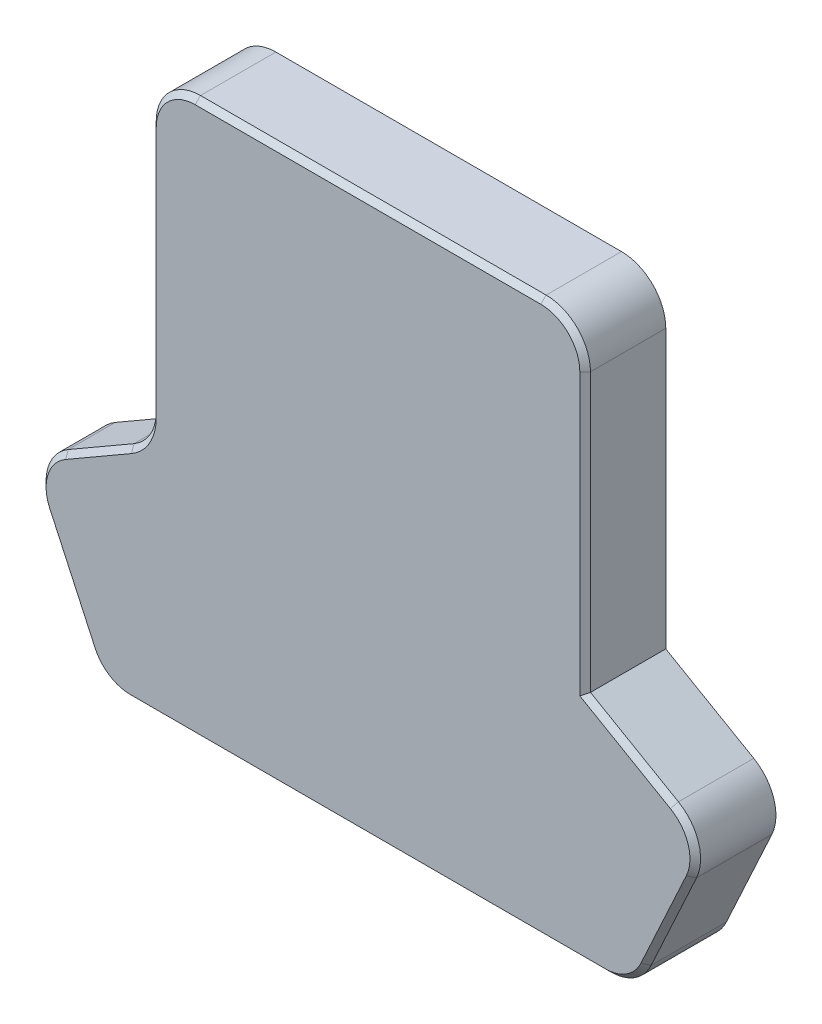
SolidWorks part; units mm, degrees
ref_plane "Front Plane" through (0, 0, 0) normal (0, 0, 1) x (1, 0, 0)
ref_plane "Top Plane" through (0, 0, 0) normal (0, 1, 0) x (1, 0, 0)
ref_plane "Right Plane" through (0, 0, 0) normal (1, 0, 0) x (0, 0, -1)
sketch "Sketch1" plane through (0, 0, 0) normal (0, 0, 1) x (1, 0, 0)
  line L0 (-54.5, 42.45) -> (-12.4, 42.45)
  line L1 (-54.5, 29.0597) -> (-54.5, 57.5) construction
  line L2 (-12.4, 42.45) -> (-12.4, 7.25)
  line L3 (-12.4, 7.25) -> (-63.3441, 7.25)
  line L4 (-60, 0) -> (-68.3768, 18.1612) construction
  line L5 (-54.5, 42.45) -> (-54.5, 62.5)
  line L6 (-54.5, 62.5) -> (-5.5, 62.5)
  line L7 (-5.5, 62.5) -> (-5.5, 26.173)
  line L8 (-5.5, 26.173) -> (8.3768, 18.1612)
  line L9 (8.3768, 18.1612) -> (0, 0)
  line L10 (0, 0) -> (-60, 0)
  line L11 (-60, 0) -> (-63.3441, 7.25)
  line L12 (-71.5, 7.35) -> (-13.5, 7.35) construction
  line L13 (-3, 24.7296) -> (4.4256, 20.4425) construction
  line L14 (0, 0) -> (8.3768, 18.1612) construction
  line L16 (-12.5, 8.35) -> (-12.5, 41.35) construction
  line L17 (-13.5, 42.35) -> (-71.5, 42.35) construction
  point P14 (0, 0)
  point P15 (4.5312, 0)
  dimension "D1" = 0.1
  dimension "0.1" = 0.1
  dimension "D2" = 0.1
extrude "Boss-Extrude1" add sketch "Sketch1" along normal offset from surface (3.2 mm away) 0.2
sketch "Sketch2" plane through (0, 0, 3.2) normal (0, 0, 1) x (1, 0, 0)
  line L0 (-5.5, 26.173) -> (-5.5, 62.5)
  line L1 (-5.5, 62.5) -> (-54.5, 62.5)
  line L2 (-54.5, 62.5) -> (-54.5, 26.173)
  line L3 (-54.5, 26.173) -> (-68.3768, 18.1612)
  line L4 (-68.3768, 18.1612) -> (-60, 0)
  line L5 (-60, 0) -> (0, 0)
  line L6 (0, 0) -> (8.3768, 18.1612)
  line L7 (8.3768, 18.1612) -> (-5.5, 26.173)
  line L8 (-64.4256, 20.4425) -> (-57, 24.7296) construction
  line L9 (-61.3403, 2.9058) -> (-66.4659, 14.0181) construction
  line L10 (-54.5, 29.0597) -> (-54.5, 57.5) construction
  line L11 (-35.5, 33.05) -> (-35.5, 16.35) construction
  line L12 (-15.5, 38.85) -> (-35.5, 38.85)
  line L13 (-15.5, 38.85) -> (-15.5, 10.85)
  line L14 (-15.5, 10.85) -> (-35.5, 10.85)
  line L15 (-35.5, 38.85) -> (-35.5, 10.85)
  line L16 (-22.5, 38.85) -> (-32.5, 38.85) construction
  line L18 (-32.5, 10.85) -> (-22.5, 10.85) construction
  line L19 (-15.5, 17.35) -> (-15.5, 32.05) construction
extrude "Boss-Extrude2" add sketch "Sketch2" along normal offset from surface (4.9 mm away) 0.1
sketch "Sketch3" plane through (0, 0, 8.1) normal (0, 0, 1) x (1, 0, 0)
  line L0 (-68.3768, 18.1612) -> (-60, 0)
  line L1 (-60, 0) -> (0, 0)
  line L2 (0, 0) -> (8.3768, 18.1612)
  line L3 (8.3768, 18.1612) -> (-5.5, 26.173)
  line L4 (-5.5, 26.173) -> (-5.5, 62.5)
  line L5 (-5.5, 62.5) -> (-54.5, 62.5)
  line L6 (-54.5, 62.5) -> (-54.5, 26.173)
  line L7 (-54.5, 26.173) -> (-68.3768, 18.1612)
extrude "Boss-Extrude3" add sketch "Sketch3" along normal blind 1
fillet "Fillet1" radius 5 7 edges at (8.3768, 18.1612, 4.55) (0, 0, 4.55) (-60, 0, 4.55) (-68.3768, 18.1612, 6.15) (-54.5, 26.173, 6.15) (-5.5, 62.5, 4.55) (-54.5, 62.5, 4.55)
chamfer "Chamfer1" distance 0.6 angle 45 15 edges at (-0.5047, 0.7886, 9.1) (-30, 0, 9.1) (-59.4953, 0.7886, 9.1) (-63.9031, 8.462, 9.1) (-66.691, 17.6258, 9.1) (-60.7128, 22.586, 9.1) (-55.1699, 26.5597, 9.1) (-54.5, 43.2799, 9.1) (-53.0355, 61.0355, 9.1) (-30, 62.5, 9.1) (-6.9645, 61.0355, 9.1) (-5.5, 41.8365, 9.1) (-0.5372, 23.3077, 9.1) (6.691, 17.6258, 9.1) (3.9031, 8.462, 9.1)
